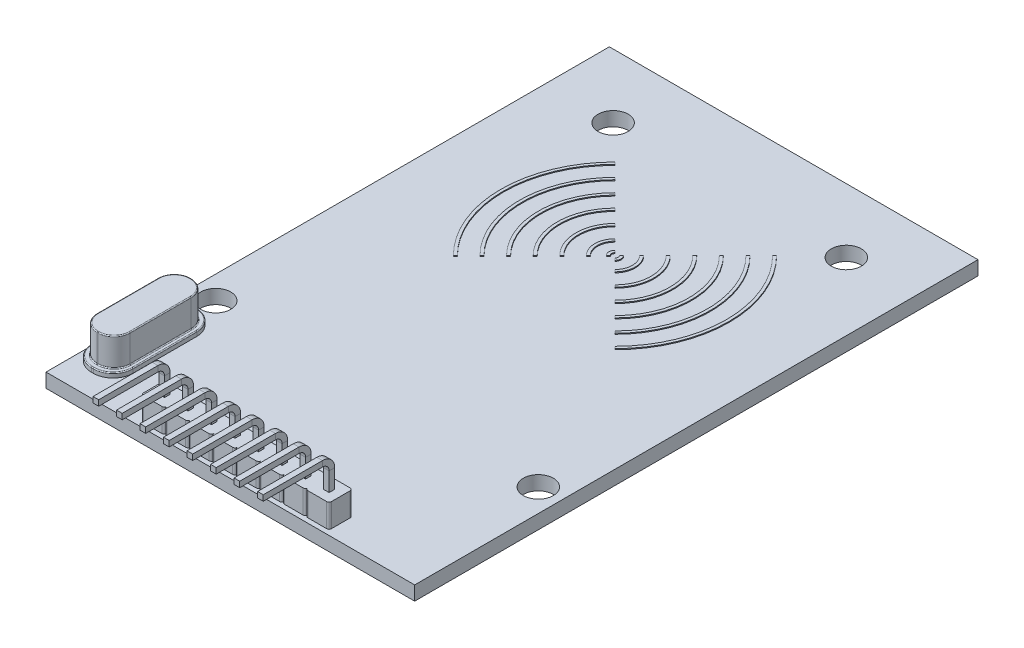
SolidWorks part; units mm, degrees
ref_plane "Front Plane" through (0, 0, 0) normal (0, 0, 1) x (1, 0, 0)
ref_plane "Top Plane" through (0, 0, 0) normal (0, 1, 0) x (1, 0, 0)
ref_plane "Right Plane" through (0, 0, 0) normal (1, 0, 0) x (0, 0, -1)
sketch "Sketch1" plane through (0, 0, 0) normal (0, 1, 0) x (1, 0, 0)
  line L1 (-19.6, 29.95) -> (19.6, 29.95)
  line L2 (-19.6, 29.95) -> (-19.6, -29.95)
  line L3 (-19.6, -29.95) -> (19.6, -29.95)
  line L4 (19.6, 29.95) -> (19.6, -29.95)
  line L5 (-19.6, 29.95) -> (19.6, -29.95) construction
  line L6 (-19.6, -29.95) -> (19.6, 29.95) construction
  point P0 (0, 0)
  dimension "D1" = 39.2
  dimension "D2" = 59.9
extrude "Boss-Extrude1" add sketch "Sketch1" along normal blind 1.5
sketch "Sketch3" plane through (0, 1.5, 0) normal (0, 1, 0) x (1, 0, 0)
  line L1 (-19.6, 29.95) -> (-19.6, -29.95) construction
  line L2 (19.6, 29.95) -> (-19.6, 29.95) construction
  line L5 (-19.6, -29.95) -> (19.6, -29.95) construction
  circle A0 centre (12.4, 23.15) radius 1.6
  circle A1 centre (-12.4, 23.15) radius 1.6
  circle A2 centre (17.15, -14.35) radius 1.6
  circle A3 centre (-17.15, -14.35) radius 1.6
  dimension "D1" = 3.2
  dimension "D2" = 24.8
  dimension "D3" = 6.8
  dimension "D4" = 7.2
  dimension "D5" = 6.8
  dimension "D6" = 34.3
  dimension "D7" = 2.45
  dimension "D8" = 15.6
  dimension "D9" = 15.6
extrude "Cut-Extrude1" cut sketch "Sketch3" against normal up to surface (1.5 mm away) up to face at (0, 0, 0)
sketch "Sketch4" plane through (0, 1.5, 0) normal (0, 1, 0) x (1, 0, 0)
  line L0 (-19.6, -29.95) -> (19.6, -29.95) construction
  line L1 (-9.75, -26.95) -> (-7.75, -26.95)
  line L2 (-10, -27.2) -> (-10, -29.2)
  line L3 (-9.75, -29.45) -> (-7.75, -29.45)
  line L5 (-19.6, 29.95) -> (-19.6, -29.95) construction
  line L7 (-7.25, -29.45) -> (-5.25, -29.45)
  line L9 (-7.25, -26.95) -> (-5.25, -26.95)
  line L11 (-4.75, -29.45) -> (-2.75, -29.45)
  line L13 (-4.75, -26.95) -> (-2.75, -26.95)
  line L15 (-2.25, -29.45) -> (-0.25, -29.45)
  line L17 (-2.25, -26.95) -> (-0.25, -26.95)
  line L19 (0.25, -29.45) -> (2.25, -29.45)
  line L21 (0.25, -26.95) -> (2.25, -26.95)
  line L23 (2.75, -29.45) -> (4.75, -29.45)
  line L25 (2.75, -26.95) -> (4.75, -26.95)
  line L27 (5.25, -29.45) -> (7.25, -29.45)
  line L29 (5.25, -26.95) -> (7.25, -26.95)
  line L30 (10, -27.2) -> (10, -29.2)
  line L31 (7.75, -29.45) -> (9.75, -29.45)
  line L33 (7.75, -26.95) -> (9.75, -26.95)
  line L34 (-7.5, -27.2) -> (-7.5, -29.2) [skipped]
  line L35 (-5, -27.2) -> (-5, -29.2) [skipped]
  line L36 (-2.5, -27.2) -> (-2.5, -29.2) [skipped]
  line L37 (0, -27.2) -> (0, -29.2) [skipped]
  line L38 (2.5, -27.2) -> (2.5, -29.2) [skipped]
  line L39 (5, -27.2) -> (5, -29.2) [skipped]
  line L40 (7.5, -27.2) -> (7.5, -29.2) [skipped]
  arc A1 (-7.75, -26.95) -> (-7.5, -27.2) centre (-7.75, -27.2) cw
  arc A2 (-7.5, -29.2) -> (-7.75, -29.45) centre (-7.75, -29.2) cw
  arc A3 (-9.75, -29.45) -> (-10, -29.2) centre (-9.75, -29.2) cw
  arc A4 (-10, -27.2) -> (-9.75, -26.95) centre (-9.75, -27.2) cw
  arc A5 (-5, -29.2) -> (-5.25, -29.45) centre (-5.25, -29.2) cw
  arc A6 (-7.25, -29.45) -> (-7.5, -29.2) centre (-7.25, -29.2) cw
  arc A7 (-7.5, -27.2) -> (-7.25, -26.95) centre (-7.25, -27.2) cw
  arc A8 (-5.25, -26.95) -> (-5, -27.2) centre (-5.25, -27.2) cw
  arc A10 (-2.5, -29.2) -> (-2.75, -29.45) centre (-2.75, -29.2) cw
  arc A11 (-4.75, -29.45) -> (-5, -29.2) centre (-4.75, -29.2) cw
  arc A12 (-5, -27.2) -> (-4.75, -26.95) centre (-4.75, -27.2) cw
  arc A13 (-2.75, -26.95) -> (-2.5, -27.2) centre (-2.75, -27.2) cw
  arc A15 (0, -29.2) -> (-0.25, -29.45) centre (-0.25, -29.2) cw
  arc A16 (-2.25, -29.45) -> (-2.5, -29.2) centre (-2.25, -29.2) cw
  arc A17 (-2.5, -27.2) -> (-2.25, -26.95) centre (-2.25, -27.2) cw
  arc A18 (-0.25, -26.95) -> (0, -27.2) centre (-0.25, -27.2) cw
  arc A20 (2.5, -29.2) -> (2.25, -29.45) centre (2.25, -29.2) cw
  arc A21 (0.25, -29.45) -> (0, -29.2) centre (0.25, -29.2) cw
  arc A22 (0, -27.2) -> (0.25, -26.95) centre (0.25, -27.2) cw
  arc A23 (2.25, -26.95) -> (2.5, -27.2) centre (2.25, -27.2) cw
  arc A25 (5, -29.2) -> (4.75, -29.45) centre (4.75, -29.2) cw
  arc A26 (2.75, -29.45) -> (2.5, -29.2) centre (2.75, -29.2) cw
  arc A27 (2.5, -27.2) -> (2.75, -26.95) centre (2.75, -27.2) cw
  arc A28 (4.75, -26.95) -> (5, -27.2) centre (4.75, -27.2) cw
  arc A30 (7.5, -29.2) -> (7.25, -29.45) centre (7.25, -29.2) cw
  arc A31 (5.25, -29.45) -> (5, -29.2) centre (5.25, -29.2) cw
  arc A32 (5, -27.2) -> (5.25, -26.95) centre (5.25, -27.2) cw
  arc A33 (7.25, -26.95) -> (7.5, -27.2) centre (7.25, -27.2) cw
  arc A35 (10, -29.2) -> (9.75, -29.45) centre (9.75, -29.2) cw
  arc A36 (7.75, -29.45) -> (7.5, -29.2) centre (7.75, -29.2) cw
  arc A37 (7.5, -27.2) -> (7.75, -26.95) centre (7.75, -27.2) cw
  arc A38 (9.75, -26.95) -> (10, -27.2) centre (9.75, -27.2) cw
  point P12 (-7.5, -26.95)
  point P17 (-10, -29.45)
  point P20 (-10, -26.95)
  dimension "D7" = 0.25
  dimension "D1" = 2.5
  dimension "D2" = 2.5
  dimension "D3" = 0.5
  dimension "D4" = 9.6
  dimension "D8" = 8
extrude "Boss-Extrude3" add sketch "Sketch4" along normal blind 2.5
sketch "Sketch5" plane through (0, 4, 0) normal (0, 1, 0) x (1, 0, 0)
  line L2 (-7.75, -26.95) -> (-9.75, -26.95) construction
  line L3 (-9.05, -27.9) -> (-8.45, -27.9)
  line L4 (-9.05, -27.9) -> (-9.05, -28.5)
  line L5 (-9.05, -28.5) -> (-8.45, -28.5)
  line L6 (-8.45, -27.9) -> (-8.45, -28.5)
  line L7 (-10, -27.2) -> (-10, -29.2) construction
  line L8 (-6.55, -27.9) -> (-5.95, -27.9)
  line L9 (-5.95, -27.9) -> (-5.95, -28.5)
  line L10 (-6.55, -28.5) -> (-5.95, -28.5)
  line L11 (-6.55, -27.9) -> (-6.55, -28.5)
  line L12 (-4.05, -27.9) -> (-3.45, -27.9)
  line L13 (-3.45, -27.9) -> (-3.45, -28.5)
  line L14 (-4.05, -28.5) -> (-3.45, -28.5)
  line L15 (-4.05, -27.9) -> (-4.05, -28.5)
  line L16 (-1.55, -27.9) -> (-0.95, -27.9)
  line L17 (-0.95, -27.9) -> (-0.95, -28.5)
  line L18 (-1.55, -28.5) -> (-0.95, -28.5)
  line L19 (-1.55, -27.9) -> (-1.55, -28.5)
  line L20 (0.95, -27.9) -> (1.55, -27.9)
  line L21 (1.55, -27.9) -> (1.55, -28.5)
  line L22 (0.95, -28.5) -> (1.55, -28.5)
  line L23 (0.95, -27.9) -> (0.95, -28.5)
  line L24 (3.45, -27.9) -> (4.05, -27.9)
  line L25 (4.05, -27.9) -> (4.05, -28.5)
  line L26 (3.45, -28.5) -> (4.05, -28.5)
  line L27 (3.45, -27.9) -> (3.45, -28.5)
  line L28 (5.95, -27.9) -> (6.55, -27.9)
  line L29 (6.55, -27.9) -> (6.55, -28.5)
  line L30 (5.95, -28.5) -> (6.55, -28.5)
  line L31 (5.95, -27.9) -> (5.95, -28.5)
  line L32 (8.45, -27.9) -> (9.05, -27.9)
  line L33 (9.05, -27.9) -> (9.05, -28.5)
  line L34 (8.45, -28.5) -> (9.05, -28.5)
  line L35 (8.45, -27.9) -> (8.45, -28.5)
  dimension "D1" = 0.6
  dimension "D2" = 0.6
  dimension "D3" = 0.95
  dimension "D4" = 0.95
  dimension "D5" = 8
extrude "Cut-Extrude2" cut sketch "Sketch5" against normal up to surface (4 mm away) up to face at (-17.15, 0, 15.95)
ref_plane "Plane1" through (0, -1, 0) normal (0, -1, 0) x (-1, 0, 0)
sketch "Sketch6" plane through (0, -1, 0) normal (0, -1, 0) x (-1, 0, 0)
  line L0 (6.55, -28.5) -> (5.95, -28.5)
  line L1 (9.05, -28.5) -> (8.45, -28.5)
  line L2 (9.05, -28.5) -> (9.05, -27.9)
  line L3 (9.05, -27.9) -> (8.45, -27.9)
  line L4 (8.45, -28.5) -> (8.45, -27.9)
  line L5 (5.95, -28.5) -> (5.95, -27.9)
  line L6 (6.55, -27.9) -> (5.95, -27.9)
  line L7 (6.55, -28.5) -> (6.55, -27.9)
  line L8 (4.05, -28.5) -> (3.45, -28.5)
  line L9 (3.45, -28.5) -> (3.45, -27.9)
  line L10 (4.05, -27.9) -> (3.45, -27.9)
  line L11 (4.05, -28.5) -> (4.05, -27.9)
  line L12 (1.55, -28.5) -> (0.95, -28.5)
  line L13 (0.95, -28.5) -> (0.95, -27.9)
  line L14 (1.55, -27.9) -> (0.95, -27.9)
  line L15 (1.55, -28.5) -> (1.55, -27.9)
  line L16 (-0.95, -28.5) -> (-1.55, -28.5)
  line L17 (-1.55, -28.5) -> (-1.55, -27.9)
  line L18 (-0.95, -27.9) -> (-1.55, -27.9)
  line L19 (-0.95, -28.5) -> (-0.95, -27.9)
  line L20 (-3.45, -28.5) -> (-4.05, -28.5)
  line L21 (-4.05, -28.5) -> (-4.05, -27.9)
  line L22 (-3.45, -27.9) -> (-4.05, -27.9)
  line L23 (-3.45, -28.5) -> (-3.45, -27.9)
  line L24 (-5.95, -28.5) -> (-6.55, -28.5)
  line L25 (-6.55, -28.5) -> (-6.55, -27.9)
  line L26 (-5.95, -27.9) -> (-6.55, -27.9)
  line L27 (-5.95, -28.5) -> (-5.95, -27.9)
  line L28 (-8.45, -28.5) -> (-9.05, -28.5)
  line L29 (-9.05, -28.5) -> (-9.05, -27.9)
  line L30 (-8.45, -27.9) -> (-9.05, -27.9)
  line L31 (-8.45, -28.5) -> (-8.45, -27.9)
  dimension "D1" = 8
sketch "Sketch7" plane through (-10, 0, 0) normal (-1, 0, 0) x (0, 0, 1)
  line L0 (28.2, -1) -> (28.2, 6)
  line L1 (28.5, -1) -> (27.9, -1) construction
  line L2 (29.2, 7) -> (35.5, 7)
  arc A0 (29.2, 7) -> (28.2, 6) centre (29.2, 6) ccw
  point P7 (28.2, 7)
  dimension "D3" = 1
  dimension "D1" = 7.3
  dimension "D2" = 8
sweep "Sweep1" add profiles "Sketch6" path "Sketch7"
sketch "Sketch8" plane through (0, 1.5, 0) normal (0, 1, 0) x (1, 0, 0)
  line L0 (-19.6, -29.95) -> (19.6, -29.95) construction
  line L1 (-17.16, -16.55) -> (-16.96, -16.55)
  line L2 (-19.26, -18.65) -> (-19.26, -25.45)
  line L3 (-17.16, -27.55) -> (-16.96, -27.55)
  line L4 (-14.86, -18.65) -> (-14.86, -25.45)
  arc A0 (-19.26, -25.45) -> (-17.16, -27.55) centre (-17.16, -25.45) ccw
  arc A1 (-16.96, -27.55) -> (-14.86, -25.45) centre (-16.96, -25.45) ccw
  arc A2 (-16.96, -16.55) -> (-14.86, -18.65) centre (-16.96, -18.65) cw
  arc A3 (-17.16, -16.55) -> (-19.26, -18.65) centre (-17.16, -18.65) ccw
  point P6 (-19.26, -27.55)
  point P11 (-14.86, -16.55)
  point P14 (-19.26, -16.55)
  dimension "D3" = 2.1
  dimension "D1" = 11
  dimension "D2" = 4.4
  dimension "D4" = 2.4
extrude "Boss-Extrude4" add sketch "Sketch8" along normal blind 0.5
sketch "Sketch10" plane through (0, 2, 0) normal (0, 1, 0) x (1, 0, 0)
  line L0 (-17.06, -16.55) -> (-17.06, -27.55) construction
  line L1 (-16.96, -16.55) -> (-17.16, -16.55) construction
  line L2 (-17.16, -27.55) -> (-16.96, -27.55) construction
  line L3 (-19.26, -22.05) -> (-14.86, -22.05) construction
  line L4 (-19.26, -18.65) -> (-19.26, -25.45) construction
  line L5 (-14.86, -25.45) -> (-14.86, -18.65) construction
  line L7 (-17.11, -17.1) -> (-17.01, -17.1)
  line L8 (-18.81, -18.8) -> (-18.81, -25.3)
  line L9 (-17.11, -27) -> (-17.01, -27)
  line L10 (-15.31, -18.8) -> (-15.31, -25.3)
  line L11 (-18.81, -17.1) -> (-15.31, -27) construction
  line L12 (-18.81, -27) -> (-15.31, -17.1) construction
  arc A0 (-18.81, -25.3) -> (-17.11, -27) centre (-17.11, -25.3) ccw
  arc A1 (-17.01, -27) -> (-15.31, -25.3) centre (-17.01, -25.3) ccw
  arc A2 (-15.31, -18.8) -> (-17.01, -17.1) centre (-17.01, -18.8) ccw
  arc A3 (-17.11, -17.1) -> (-18.81, -18.8) centre (-17.11, -18.8) ccw
  point P12 (-17.06, -22.05)
  dimension "D3" = 1.7
  dimension "D1" = 3.5
  dimension "D2" = 9.9
extrude "Boss-Extrude5" add sketch "Sketch10" along normal blind 3
fillet "Fillet1" radius 0.1 24 edges at (-18.3121, 5, 17.5979) (-17.06, 5, 17.1) (-15.8079, 5, 17.5979) (-15.31, 5, 22.05) (-15.8079, 5, 26.5021) (-17.06, 5, 27) (-18.3121, 5, 26.5021) (-18.3121, 2, 17.5979) (-17.06, 2, 17.1) (-15.8079, 2, 17.5979) (-15.31, 2, 22.05) (-15.8079, 2, 26.5021) (-17.06, 2, 27) (-18.3121, 2, 26.5021) (-18.6449, 2, 17.1651) (-17.06, 2, 16.55) (-15.4751, 2, 17.1651) (-14.86, 2, 22.05) (-15.4751, 2, 26.9349) (-17.06, 2, 27.55) (-18.6449, 2, 26.9349) (-18.81, 5, 22.05) (-18.81, 2, 22.05) (-19.26, 2, 22.05)
sketch "Sketch11" plane through (0, 1.5, 0) normal (0, 1, 0) x (1, 0, 0)
  line L0 (-0.2475, 11.1975) -> (-0.4596, 11.4096)
  line L1 (-0.35, 10.95) -> (-19.6, 10.95) construction
  line L2 (-19.6, 29.95) -> (-19.6, -29.95) construction
  line L3 (19.6, 29.95) -> (-19.6, 29.95) construction
  line L4 (0.2475, 11.1975) -> (0.4596, 11.4096)
  line L5 (-0.2475, 10.7025) -> (-0.4596, 10.4904)
  line L6 (0.2475, 10.7025) -> (0.4596, 10.4904)
  line L7 (-8.4853, 19.4353) -> (-8.5913, 19.5413)
  line L8 (-8.5913, 2.3587) -> (-8.4853, 2.4647)
  line L9 (8.4853, 2.4647) -> (8.5913, 2.3587)
  line L10 (8.4853, 19.4353) -> (8.5913, 19.5413)
  line L11 (-8.3792, 19.3292) -> (-8.4853, 19.4353)
  line L12 (-6.965, 17.915) -> (-7.1771, 18.1271)
  line L13 (-5.5508, 16.5008) -> (-5.7629, 16.7129)
  line L14 (-4.1366, 15.0866) -> (-4.3487, 15.2987)
  line L15 (-2.7224, 13.6724) -> (-2.9345, 13.8845)
  line L16 (-1.3081, 12.2581) -> (-1.5203, 12.4703)
  line L17 (-1.3081, 9.6419) -> (-1.5203, 9.4297)
  line L18 (-2.7224, 8.2276) -> (-2.9345, 8.0155)
  line L19 (-4.1366, 6.8134) -> (-4.3487, 6.6013)
  line L20 (-5.5508, 5.3992) -> (-5.7629, 5.1871)
  line L21 (-8.3792, 2.5708) -> (-8.4853, 2.4647)
  line L22 (1.3081, 9.6419) -> (1.5203, 9.4297)
  line L23 (2.7224, 8.2276) -> (2.9345, 8.0155)
  line L24 (4.1366, 6.8134) -> (4.3487, 6.6013)
  line L25 (5.5508, 5.3992) -> (5.7629, 5.1871)
  line L26 (6.965, 3.985) -> (7.1771, 3.7729)
  line L27 (8.3792, 2.5708) -> (8.4853, 2.4647)
  line L28 (1.3081, 12.2581) -> (1.5203, 12.4703)
  line L29 (2.7224, 13.6724) -> (2.9345, 13.8845)
  line L30 (4.1366, 15.0866) -> (4.3487, 15.2987)
  line L31 (5.5508, 16.5008) -> (5.7629, 16.7129)
  line L32 (6.965, 17.915) -> (7.1771, 18.1271)
  line L33 (8.3792, 19.3292) -> (8.4853, 19.4353)
  line L34 (-6.965, 3.985) -> (-7.1771, 3.7729)
  arc A0 (-0.3536, 11.3036) -> (-0.3536, 10.5964) centre (0, 10.95) ccw construction
  arc A1 (-1.4142, 12.3642) -> (-1.4142, 9.5358) centre (0, 10.95) ccw construction
  arc A2 (-2.8284, 13.7784) -> (-2.8284, 8.1216) centre (0, 10.95) ccw construction
  arc A3 (-4.2426, 15.1926) -> (-4.2426, 6.7074) centre (0, 10.95) ccw construction
  arc A4 (-5.6569, 16.6069) -> (-5.6569, 5.2931) centre (0, 10.95) ccw construction
  arc A5 (-5.6569, 16.6069) -> (-5.6569, 5.2931) centre (0, 10.95) ccw
  arc A6 (-7.0711, 18.0211) -> (-7.0711, 3.8789) centre (0, 10.95) ccw construction
  arc A7 (-8.4853, 19.4353) -> (-8.4853, 2.4647) centre (0, 10.95) ccw construction
  arc A8 (0.3536, 10.5964) -> (0.3536, 11.3036) centre (0, 10.95) ccw construction
  arc A9 (1.4142, 9.5358) -> (1.4142, 12.3642) centre (0, 10.95) ccw construction
  arc A10 (2.8284, 8.1216) -> (2.8284, 13.7784) centre (0, 10.95) ccw construction
  arc A11 (4.2426, 6.7074) -> (4.2426, 15.1926) centre (0, 10.95) ccw construction
  arc A12 (5.6569, 5.2931) -> (5.6569, 16.6069) centre (0, 10.95) ccw construction
  arc A13 (5.6569, 5.2931) -> (5.6569, 16.6069) centre (0, 10.95) ccw
  arc A14 (7.0711, 3.8789) -> (7.0711, 18.0211) centre (0, 10.95) ccw construction
  arc A15 (8.4853, 2.4647) -> (8.4853, 19.4353) centre (0, 10.95) ccw construction
  arc A16 (-8.5913, 19.5413) -> (-8.5913, 2.3587) centre (0, 10.95) ccw
  arc A17 (-7.1771, 18.1271) -> (-7.1771, 3.7729) centre (0, 10.95) ccw
  arc A18 (-5.7629, 16.7129) -> (-5.7629, 5.1871) centre (0, 10.95) ccw
  arc A19 (-4.3487, 15.2987) -> (-4.3487, 6.6013) centre (0, 10.95) ccw
  arc A20 (-2.9345, 13.8845) -> (-2.9345, 8.0155) centre (0, 10.95) ccw
  arc A21 (-1.5203, 12.4703) -> (-1.5203, 9.4297) centre (0, 10.95) ccw
  arc A22 (-0.4596, 11.4096) -> (-0.4596, 10.4904) centre (0, 10.95) ccw
  arc A23 (0.4596, 10.4904) -> (0.4596, 11.4096) centre (0, 10.95) ccw
  arc A24 (1.5203, 9.4297) -> (1.5203, 12.4703) centre (0, 10.95) ccw
  arc A25 (2.9345, 8.0155) -> (2.9345, 13.8845) centre (0, 10.95) ccw
  arc A26 (4.3487, 6.6013) -> (4.3487, 15.2987) centre (0, 10.95) ccw
  arc A27 (5.7629, 5.1871) -> (5.7629, 16.7129) centre (0, 10.95) ccw
  arc A28 (7.1771, 3.7729) -> (7.1771, 18.1271) centre (0, 10.95) ccw
  arc A29 (8.5913, 2.3587) -> (8.5913, 19.5413) centre (0, 10.95) ccw
  arc A30 (-8.3792, 19.3292) -> (-8.3792, 2.5708) centre (0, 10.95) ccw
  arc A31 (-6.965, 17.915) -> (-6.965, 3.985) centre (0, 10.95) ccw
  arc A32 (-5.5508, 16.5008) -> (-5.5508, 5.3992) centre (0, 10.95) ccw
  arc A33 (-4.1366, 15.0866) -> (-4.1366, 6.8134) centre (0, 10.95) ccw
  arc A34 (-2.7224, 13.6724) -> (-2.7224, 8.2276) centre (0, 10.95) ccw
  arc A35 (-1.3081, 12.2581) -> (-1.3081, 9.6419) centre (0, 10.95) ccw
  arc A36 (-0.2475, 11.1975) -> (-0.2475, 10.7025) centre (0, 10.95) ccw
  arc A37 (0.2475, 10.7025) -> (0.2475, 11.1975) centre (0, 10.95) ccw
  arc A38 (1.3081, 9.6419) -> (1.3081, 12.2581) centre (0, 10.95) ccw
  arc A39 (2.7224, 8.2276) -> (2.7224, 13.6724) centre (0, 10.95) ccw
  arc A40 (4.1366, 6.8134) -> (4.1366, 15.0866) centre (0, 10.95) ccw
  arc A41 (5.5508, 5.3992) -> (5.5508, 16.5008) centre (0, 10.95) ccw
  arc A42 (6.965, 3.985) -> (6.965, 17.915) centre (0, 10.95) ccw
  arc A43 (8.3792, 2.5708) -> (8.3792, 19.3292) centre (0, 10.95) ccw
  dimension "D1" = 45
  dimension "D2" = 0.5
  dimension "D3" = 2
  dimension "D4" = 6
  dimension "D5" = 10
  dimension "D6" = 19
  dimension "D10" = 8
  dimension "D11" = 4
  dimension "D12" = 12
  dimension "D7" = 45
  dimension "D8" = 45
  dimension "D9" = 45
  dimension "D13" = 0.15
  dimension "D14" = 0.15
extrude "Boss-Extrude6" add sketch "Sketch11" along normal blind 0.1 contours A16 L8 L21 A30 L11 L7 | A17 L34 A31 L12 | A18 L20 A32 L13 | A19 L19 A33 L14 | A20 L18 A34 L15 | A35 L17 A21 L16 | A36 L5 A22 L0 | A23 L4 A37 L6 | A24 L28 A38 L22 | A25 L29 A39 L23 | A26 L30 A40 L24 | A27 L31 A41 L25 | A28 L32 A42 L26 | A29 L10 L33 A43 L27 L9
